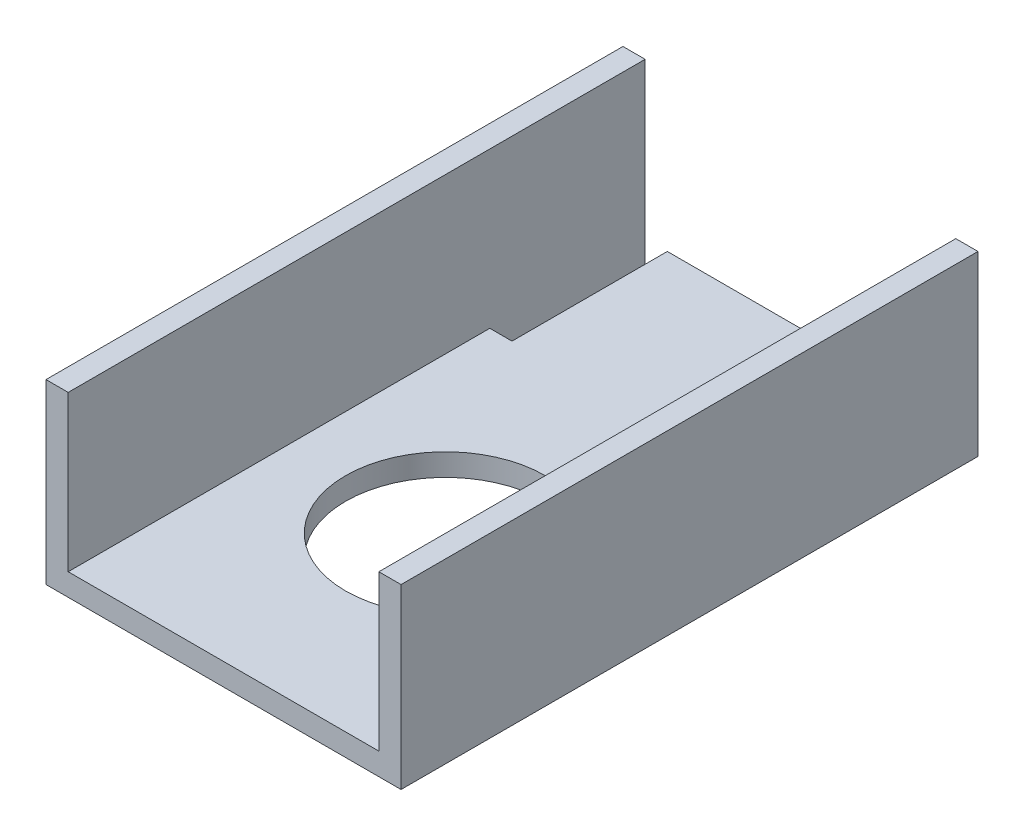
SolidWorks part; units mm, degrees
material "6063-T6"
ref_plane "Front" through (0, 0, 0) normal (0, 0, 1) x (1, 0, 0)
ref_plane "Top" through (0, 0, 0) normal (0, 1, 0) x (1, 0, 0)
ref_plane "Right" through (0, 0, 0) normal (1, 0, 0) x (0, 0, -1)
sketch "Sketch1" plane through (0, 0, 0) normal (0, 0, 1) x (1, 0, 0)
  line L0 (47.625, 3.175) -> (47.625, 25.4)
  line L1 (0, 0) -> (50.8, 0)
  line L2 (0, 0) -> (0, 25.4)
  line L4 (50.8, 0) -> (50.8, 25.4)
  line L5 (3.175, 3.175) -> (47.625, 3.175)
  line L6 (3.175, 3.175) -> (3.175, 25.4)
  line L7 (50.8, 25.4) -> (47.625, 25.4)
  line L8 (0, 25.4) -> (3.175, 25.4)
  dimension "D1" = 25.4
  dimension "D2" = 50.8
  dimension "D3" = 3.175
extrude "Boss-Extrude1" add sketch "Sketch1" along normal blind 82.55
sketch "Sketch2" plane through (0, 0, 0) normal (0, -1, 0) x (1, 0, 0)
  line L0 (25.4, 50.8) -> (25.4, 82.55) construction
  line L1 (0, 82.55) -> (50.8, 82.55) construction
  circle A0 centre (25.4, 50.8) radius 14.2875
  dimension "D1" = 28.575
  dimension "D2" = 31.75
extrude "Cut-Extrude1" cut sketch "Sketch2" against normal up to next
sketch "Sketch3" plane through (0, 3.175, 0) normal (0, 1, 0) x (1, 0, 0)
  line L0 (3.175, -82.55) -> (3.175, 0) construction
  line L1 (3.175, -22.225) -> (6.35, -22.225)
  line L2 (3.175, -22.225) -> (3.175, 0)
  line L3 (3.175, 0) -> (6.35, 0)
  line L4 (6.35, -22.225) -> (6.35, 0)
  line L5 (3.175, -22.225) -> (6.35, 0) construction
  line L6 (3.175, 0) -> (6.35, -22.225) construction
  point P4 (4.7625, -11.1125)
  dimension "D1" = 22.225
  dimension "D2" = 3.175
extrude "Cut-Extrude2" cut sketch "Sketch3" against normal up to next
